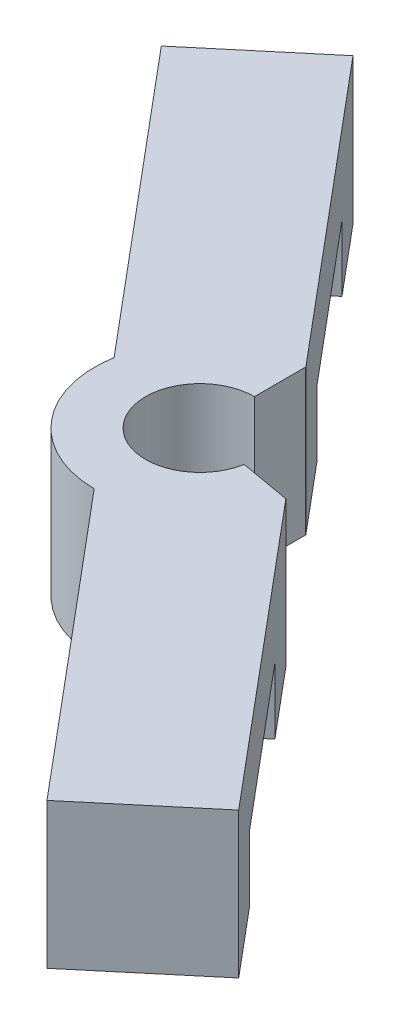
SolidWorks part; units mm, degrees
ref_plane "Front Plane" through (0, 0, 0) normal (0, 0, 1) x (1, 0, 0)
ref_plane "Top Plane" through (0, 0, 0) normal (0, 1, 0) x (1, 0, 0)
ref_plane "Right Plane" through (0, 0, 0) normal (1, 0, 0) x (0, 0, -1)
sketch "Sketch1" plane through (0, 0, 0) normal (0, 1, 0) x (1, 0, 0)
  line L0 (0, 3.2) -> (0, 6.2)
  line L1 (3.1514, -0.5557) -> (6.1058, -1.0766)
  line L2 (-17.5243, 20.8846) -> (17.5243, -20.8846)
  line L3 (-0.0192, -6.2) -> (14.4601, -23.4558)
  line L4 (6.1091, -1.0577) -> (20.5884, -18.3135)
  line L5 (14.4601, -23.4558) -> (20.5884, -18.3135)
  line L7 (-6.1091, 1.0577) -> (-20.5884, 18.3135)
  line L8 (-20.5884, 18.3135) -> (-14.4601, 23.4558)
  line L9 (0.0192, 6.2) -> (-14.4601, 23.4558)
  line L11 (0, 0) -> (10.9987, 9.229) construction
  line L12 (-7.2204, 14.8279) -> (-13.3488, 9.6856) construction
  circle A0 centre (0, 0) radius 6.2
  circle A1 centre (0, 0) radius 3.2
  arc A3 (-0.0192, -6.2) -> (3.9853, -4.7495) centre (0, 0) cw
  arc A4 (-6.1091, 1.0577) -> (-3.9853, 4.7495) centre (0, 0) ccw
  point P11 (0, 0)
  point P13 (-5.3492, 0.0934)
  point P15 (-4.3493, 0.0759)
  point P18 (-0.0192, -6.2)
  point P19 (0, 0)
  point P26 (-0.0247, 0.0404)
  point P27 (0, 0)
  point P30 (0, 0)
  dimension "D1" = 3
  dimension "D3" = 12.4
  dimension "D6" = 6.4
  dimension "D5" = 16
  dimension "D2" = 100
  dimension "D4" = 8
extrude "Boss-Extrude2" add sketch "Sketch1" along normal blind 8.55
sketch "Sketch2" plane through (-3.0642, 0, 2.5712) normal (-0.766, 0, 0.6428) x (0.6428, 0, 0.766)
  line L0 (-16, 8.55) -> (-16, 0) construction
  line L1 (-4.7371, 8.55) -> (-27.2629, 8.55) construction
  line L2 (-4.7371, 0) -> (-27.2629, 0) construction
  line L3 (0, 0) -> (0, 8.55) construction
  line L4 (-4.7371, 0) -> (4.7371, 0) construction
  line L5 (4.7371, 8.55) -> (-4.7371, 8.55) construction
  line L6 (-22, 0) -> (-22, 3.8724)
  line L7 (-22, 3.8724) -> (-10, 3.8724)
  line L8 (-10, 3.8724) -> (-10, 0)
  line L9 (-10, 0) -> (-22, 0)
  line L11 (10, 3.8724) -> (10, 0)
  line L12 (22, 3.8724) -> (10, 3.8724)
  line L13 (22, 0) -> (22, 3.8724)
  line L14 (10, 0) -> (22, 0)
  line L15 (-16, 8.55) -> (-16, 0) construction
  dimension "D1" = 16
  dimension "D2" = 12
extrude "Cut-Extrude1" cut sketch "Sketch2" against normal blind 10
